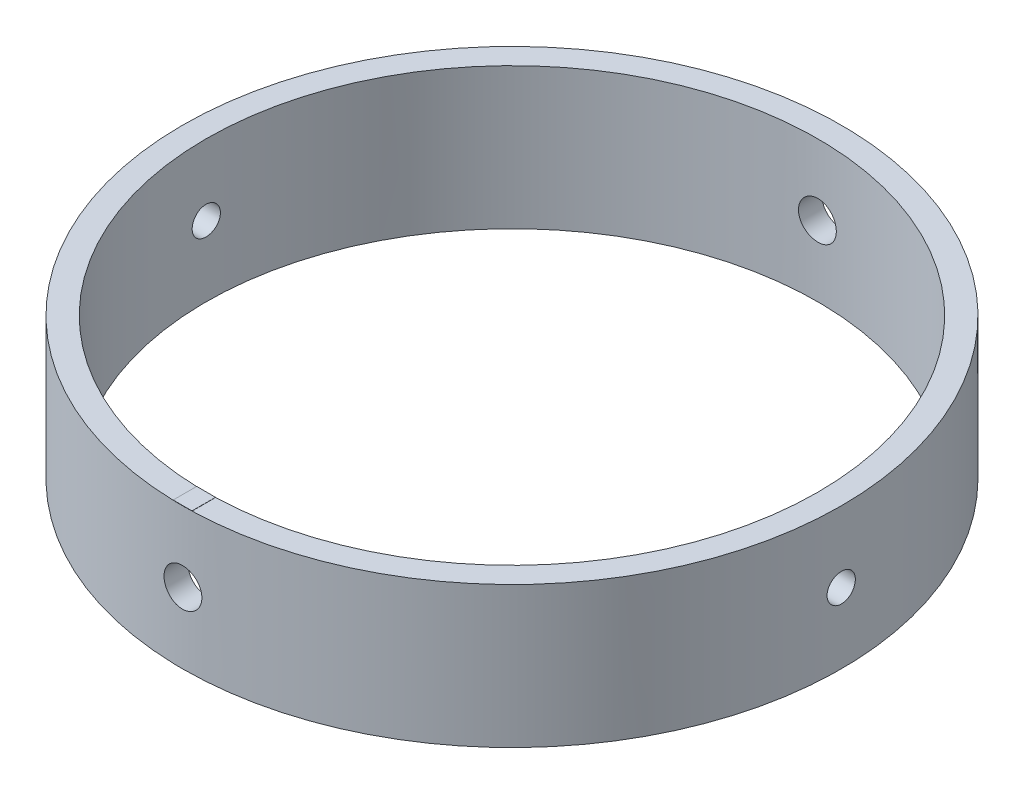
SolidWorks part; units mm, degrees
ref_plane "Front Plane" through (0, 0, 0) normal (0, 0, 1) x (1, 0, 0)
ref_plane "Top Plane" through (0, 0, 0) normal (0, 1, 0) x (1, 0, 0)
ref_plane "Right Plane" through (0, 0, 0) normal (1, 0, 0) x (0, 0, -1)
sketch "Sketch1" plane through (0, 0, 0) normal (0, 1, 0) x (1, 0, 0)
  circle A0 centre (0, 0) radius 44.45
  circle A1 centre (0, 0) radius 41.275
  dimension "D1" = 88.9
  dimension "D2" = 82.55
extrude "Boss-Extrude1" add sketch "Sketch1" along normal blind 19.05
ref_plane "Plane1" through (0, 0, 31.75) normal (0, 0, 1) x (1, 0, 0)
ref_plane "Plane2" through (0, 0, -31.75) normal (0, 0, 1) x (1, 0, 0)
sketch "Sketch3" plane through (0, 0, 31.75) normal (0, 0, 1) x (1, 0, 0)
  line L0 (41.275, 19.05) -> (-41.275, 19.05) construction
  circle A0 centre (0, 9.525) radius 2.7224
  dimension "D1" = 9.525
hole_wizard "Tap Drill for 1/4-20 Tap1" positions "Sketch4" profile "Sketch5" hole size "1/4-20" standard "ANSI Inch"
sketch "Sketch4" plane through (0, 0, 31.75) normal (0, 0, 1) x (1, 0, 0)
  point P0 (0, 9.525)
sketch "Sketch5" plane through (0, 9.525, 31.75) normal (1, 0, 0) x (0, -1, 0)
  line L0 (0, 0) -> (0, 76.2)
  line L1 (0, 76.2) -> (2.5527, 76.2)
  line L2 (2.5527, 76.2) -> (2.5527, 0)
  line L5 (2.5527, 0) -> (0, 0)
  line L11 (0, -6.35) -> (0, 107.95) construction
  dimension "Thru Hole Dia." = 5.1054
  dimension "Thru Hole Depth" = 76.2
sketch "Sketch7" plane through (0, 0, -31.75) normal (0, 0, 1) x (1, 0, 0)
  line L0 (44.45, 19.05) -> (-44.45, 19.05) construction
  circle A0 centre (0, 9.525) radius 3.5632
  dimension "D1" = 9.525
hole_wizard "Tap Drill for 1/4-20 Tap2" positions "Sketch8" profile "Sketch9" hole size "1/4-20" standard "ANSI Inch" end condition up to next
sketch "Sketch8" plane through (0, 0, -31.75) normal (0, 0, 1) x (1, 0, 0)
  point P0 (0, 9.525)
sketch "Sketch9" plane through (0, 9.525, -31.75) normal (1, 0, 0) x (0, 1, 0)
  line L0 (0, 0) -> (0, 76.2)
  line L1 (0, 76.2) -> (2.5527, 76.2)
  line L2 (2.5527, 76.2) -> (2.5527, 0)
  line L5 (2.5527, 0) -> (0, 0)
  line L11 (0, -6.35) -> (0, 107.95) construction
  dimension "Thru Hole Dia." = 5.1054
  dimension "Thru Hole Depth" = 76.2
ref_plane "Plane3" through (31.75, 0, 0) normal (1, 0, 0) x (0, 0, -1)
ref_plane "Plane4" through (-31.75, 0, 0) normal (1, 0, 0) x (0, 0, -1)
sketch "Sketch10" plane through (-31.75, 0, 0) normal (1, 0, 0) x (0, 0, -1)
  circle A0 centre (0, 9.4879) radius 1.905
  dimension "D1" = 3.81
extrude "Cut-Extrude3" cut sketch "Sketch10" against normal through all and the other way through all
sketch3d "3DSketch1"
  point P0 (40.508, 8.9339, 18.3005)
sketch "TigWeld" plane through (0, 19.05, 0) normal (0, 1, 0) x (1, 0, 0)
  line L0 (1.2712, -44.4318) -> (1.2712, -41.2554)
  line L1 (1.2712, -41.2554) -> (-1.2712, -41.2554)
  line L2 (-1.2712, -41.2554) -> (-1.2712, -44.4318)
  line L3 (-1.2712, -44.4318) -> (1.2712, -44.4318)
  circle A0 centre (0, 0) radius 44.45 construction
  circle A1 centre (0, 0) radius 41.275 construction
  point P6 (0, 0)
extrude "Boss-Extrude2" add sketch "TigWeld" along normal blind 0.0254
